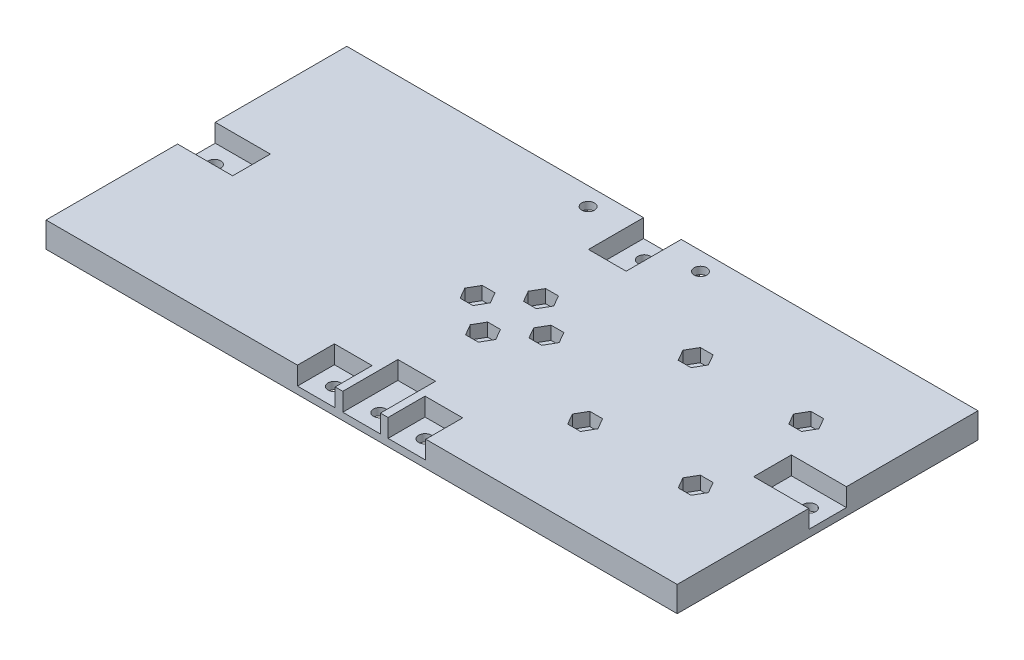
SolidWorks part; units mm, degrees
ref_plane "Front Plane" through (0, 0, 0) normal (0, 0, 1) x (1, 0, 0)
ref_plane "Top Plane" through (0, 0, 0) normal (0, 1, 0) x (1, 0, 0)
ref_plane "Right Plane" through (0, 0, 0) normal (1, 0, 0) x (0, 0, -1)
sketch "Sketch1" plane through (0, 0, 0) normal (0, 1, 0) x (1, 0, 0)
  line L1 (0, 0) -> (174.17, 0)
  line L2 (0, 0) -> (0, 83)
  line L3 (0, 83) -> (174.17, 83)
  line L4 (174.17, 0) -> (174.17, 83)
  dimension "D1" = 174.17
  dimension "D2" = 83
extrude "Boss-Extrude1" add sketch "Sketch1" along normal blind 7
sketch "Sketch2" plane through (0, 7, 0) normal (0, 1, 0) x (1, 0, 0)
  line L0 (0, 83) -> (174.17, 0) construction
  line L1 (77.585, 41.5) -> (96.585, 41.5) construction
  line L2 (87.085, 49.5) -> (87.085, 33.5) construction
  circle A0 centre (87.085, 49.5) radius 1.75
  circle A1 centre (77.585, 41.5) radius 1.75
  circle A2 centre (96.585, 41.5) radius 1.75
  circle A3 centre (87.085, 33.5) radius 1.75
  point P8 (87.085, 41.5)
  point P9 (87.085, 41.5)
  point P10 (87.085, 41.5)
  dimension "D3" = 3.5
  dimension "D1" = 19
  dimension "D2" = 16
extrude "Cut-Extrude1" cut sketch "Sketch2" against normal through all
sketch "Sketch3" plane through (0, 7, 0) normal (0, 1, 0) x (1, 0, 0)
  line L0 (0, 83) -> (174.17, 0) construction
  line L1 (5, 41.5) -> (169.17, 41.5) construction
  line L2 (87.085, 78) -> (87.085, 5) construction
  circle A0 centre (87.085, 78) radius 1.75
  circle A1 centre (5, 41.5) radius 1.75
  circle A2 centre (87.085, 5) radius 1.75
  circle A3 centre (169.17, 41.5) radius 1.75
  point P8 (87.085, 41.5)
  point P9 (87.085, 41.5)
  point P11 (87.085, 41.5)
  dimension "D3" = 3.5
  dimension "D1" = 164.17
  dimension "D2" = 73
extrude "Cut-Extrude2" cut sketch "Sketch3" against normal through all
sketch "Sketch4" plane through (0, 7, 0) normal (0, 1, 0) x (1, 0, 0)
  line L0 (0, 83) -> (0, 0) construction
  line L1 (0, 46.5) -> (15, 46.5) construction
  line L2 (0, 46.5) -> (0, 36.5) construction
  line L3 (0, 36.5) -> (15, 36.5) construction
  line L4 (15, 46.5) -> (15, 36.5) construction
  line L5 (0, 0) -> (174.17, 0) construction
  line L6 (82.085, 0) -> (92.085, 0) construction
  line L7 (82.085, 0) -> (82.085, 15) construction
  line L8 (82.085, 15) -> (92.085, 15) construction
  line L9 (92.085, 0) -> (92.085, 15) construction
  line L10 (174.17, 83) -> (0, 83) construction
  line L11 (92.085, 83) -> (82.085, 83) construction
  line L12 (92.085, 83) -> (92.085, 68) construction
  line L13 (92.085, 68) -> (82.085, 68) construction
  line L14 (82.085, 83) -> (82.085, 68) construction
  line L15 (174.17, 0) -> (174.17, 83) construction
  line L16 (174.17, 36.5) -> (159.17, 36.5) construction
  line L17 (174.17, 36.5) -> (174.17, 46.5) construction
  line L18 (174.17, 46.5) -> (159.17, 46.5) construction
  line L19 (159.17, 36.5) -> (159.17, 46.5) construction
  line L20 (0, 41.5) -> (174.17, 41.5) construction
  line L21 (87.085, 83) -> (87.085, 0) construction
  line L22 (-0.2, 46.7) -> (15.2, 46.7)
  line L23 (15.2, 46.7) -> (15.2, 36.3)
  line L24 (-0.2, 36.3) -> (15.2, 36.3)
  line L25 (-0.2, 46.7) -> (-0.2, 36.3)
  line L26 (81.885, 15.2) -> (92.285, 15.2)
  line L27 (92.285, -0.2) -> (92.285, 15.2)
  line L28 (81.885, -0.2) -> (92.285, -0.2)
  line L29 (81.885, -0.2) -> (81.885, 15.2)
  line L30 (81.885, 83.2) -> (81.885, 67.8)
  line L31 (92.285, 67.8) -> (81.885, 67.8)
  line L32 (92.285, 83.2) -> (92.285, 67.8)
  line L33 (92.285, 83.2) -> (81.885, 83.2)
  line L34 (174.37, 46.7) -> (158.97, 46.7)
  line L35 (158.97, 36.3) -> (158.97, 46.7)
  line L36 (174.37, 36.3) -> (158.97, 36.3)
  line L37 (174.37, 36.3) -> (174.37, 46.7)
  point P26 (87.085, 0)
  point P27 (0, 41.5)
  point P28 (87.085, 83)
  point P29 (174.17, 41.5)
  dimension "D1" = 15
  dimension "D2" = 10
  dimension "D3" = 0.2
extrude "Cut-Extrude3" cut sketch "Sketch4" against normal blind 5
sketch "Sketch5" plane through (0, 7, 0) normal (0, 1, 0) x (1, 0, 0)
  line L0 (0, 0) -> (81.885, 0) construction
  line L6 (79.585, 10) -> (79.585, 0) construction
  line L7 (79.585, 0) -> (69.585, 0) construction
  line L9 (79.585, 10) -> (69.585, 10) construction
  line L10 (69.585, 0) -> (69.585, 10) construction
  line L11 (94.585, 0) -> (104.585, 0) construction
  line L13 (94.585, 10) -> (104.585, 10) construction
  line L14 (104.585, 0) -> (104.585, 10) construction
  line L16 (92.285, 0) -> (174.17, 0) construction
  line L17 (94.585, 10) -> (94.585, 0) construction
  line L18 (79.585, 0) -> (94.585, 0) construction
  line L22 (87.085, 83) -> (87.085, 0) construction
  line L23 (92.285, 83) -> (81.885, 83) construction
  line L24 (79.785, 10.2) -> (69.385, 10.2)
  line L25 (69.385, -0.2) -> (69.385, 10.2)
  line L26 (79.785, -0.2) -> (69.385, -0.2)
  line L27 (79.785, 10.2) -> (79.785, -0.2)
  line L28 (94.385, 10.2) -> (104.785, 10.2)
  line L29 (104.785, -0.2) -> (104.785, 10.2)
  line L30 (94.385, -0.2) -> (104.785, -0.2)
  line L31 (94.385, 10.2) -> (94.385, -0.2)
  point P2 (87.085, 0)
  dimension "D1" = 15
  dimension "D2" = 0.2
  dimension "D3" = 10
  dimension "D4" = 10
  dimension "D5" = 10
  dimension "D6" = 10
extrude "Cut-Extrude4" cut sketch "Sketch5" against normal blind 5
sketch "Sketch6" plane through (0, 2, 0) normal (0, 1, 0) x (1, 0, 0)
  line L0 (74.585, 0) -> (74.585, 5) construction
  line L1 (79.785, 0) -> (69.385, 0) construction
  line L2 (99.585, 0) -> (99.585, 5) construction
  line L3 (94.385, 0) -> (104.785, 0) construction
  circle A0 centre (74.585, 5) radius 1.75
  circle A1 centre (99.585, 5) radius 1.75
  dimension "D3" = 3.5
  dimension "D4" = 3.5
  dimension "D1" = 5
  dimension "D2" = 5
extrude "Cut-Extrude5" cut sketch "Sketch6" against normal through all
sketch "ESC Reference" plane through (0, 0, 0) normal (0, -1, 0) x (1, 0, 0)
  line L0 (174.17, -41.5) -> (87.1154, -41.5) construction
  line L1 (116.7639, -20.5) -> (158.7639, -20.5) construction
  line L2 (116.7639, -20.5) -> (116.7639, -62.5) construction
  line L3 (116.7639, -62.5) -> (158.7639, -62.5) construction
  line L4 (158.7639, -20.5) -> (158.7639, -62.5) construction
  line L5 (122.5139, -26.25) -> (153.0139, -26.25) construction
  line L6 (122.5139, -26.25) -> (122.5139, -56.75) construction
  line L7 (122.5139, -56.75) -> (153.0139, -56.75) construction
  line L8 (153.0139, -26.25) -> (153.0139, -56.75) construction
  line L9 (174.17, 0) -> (174.17, -83) construction
  point P4 (159.4552, -57.2836)
  point P9 (158.7639, -41.5)
  point P10 (122.5139, -41.5)
  point P11 (116.7639, -41.5)
  point P12 (137.7639, -26.25)
  point P13 (137.7639, -20.5)
  point P14 (164.0651, -62.5)
  dimension "D1" = 42
  dimension "D2" = 42
  dimension "D3" = 30.5
  dimension "D4" = 30.5
  dimension "D5" = 21.1561
sketch "Sketch12" plane through (0, 0, 0) normal (0, -1, 0) x (1, 0, 0)
  circle A0 centre (122.5139, -26.25) radius 1.75
  circle A1 centre (153.0139, -26.25) radius 1.75
  circle A2 centre (122.5139, -56.75) radius 1.75
  circle A3 centre (153.0139, -56.75) radius 1.75
  dimension "D1" = 3.5
extrude "Cut-Extrude9" cut sketch "Sketch12" against normal through all
sketch "Sketch7" plane through (0, 7, 0) normal (0, 1, 0) x (1, 0, 0)
  line L0 (75.8241, 44.55) -> (79.3459, 44.55)
  line L1 (79.3459, 44.55) -> (81.1068, 41.5)
  line L2 (81.1068, 41.5) -> (79.3459, 38.45)
  line L3 (79.3459, 38.45) -> (75.8241, 38.45)
  line L4 (75.8241, 38.45) -> (74.0632, 41.5)
  line L5 (74.0632, 41.5) -> (75.8241, 44.55)
  line L6 (87.085, 33.5) -> (87.085, 49.5) construction
  line L7 (85.3241, 52.55) -> (88.8459, 52.55)
  line L8 (88.8459, 52.55) -> (90.6068, 49.5)
  line L9 (90.6068, 49.5) -> (88.8459, 46.45)
  line L10 (88.8459, 46.45) -> (85.3241, 46.45)
  line L11 (85.3241, 46.45) -> (83.5632, 49.5)
  line L12 (83.5632, 49.5) -> (85.3241, 52.55)
  line L13 (77.585, 41.5) -> (96.585, 41.5) construction
  line L14 (100.1068, 41.5) -> (98.3459, 44.55)
  line L15 (98.3459, 38.45) -> (100.1068, 41.5)
  line L16 (94.8241, 38.45) -> (98.3459, 38.45)
  line L17 (93.0632, 41.5) -> (94.8241, 38.45)
  line L18 (94.8241, 44.55) -> (93.0632, 41.5)
  line L19 (98.3459, 44.55) -> (94.8241, 44.55)
  line L20 (83.5632, 33.5) -> (85.3241, 30.45)
  line L21 (85.3241, 36.55) -> (83.5632, 33.5)
  line L22 (88.8459, 36.55) -> (85.3241, 36.55)
  line L23 (90.6068, 33.5) -> (88.8459, 36.55)
  line L24 (88.8459, 30.45) -> (90.6068, 33.5)
  line L25 (85.3241, 30.45) -> (88.8459, 30.45)
  line L26 (120.753, 29.3) -> (124.2749, 29.3)
  line L27 (124.2749, 29.3) -> (126.0358, 26.25)
  line L28 (126.0358, 26.25) -> (124.2749, 23.2)
  line L29 (124.2749, 23.2) -> (120.753, 23.2)
  line L30 (120.753, 23.2) -> (118.9921, 26.25)
  line L31 (118.9921, 26.25) -> (120.753, 29.3)
  line L32 (151.253, 29.3) -> (154.7749, 29.3)
  line L33 (154.7749, 29.3) -> (156.5358, 26.25)
  line L34 (156.5358, 26.25) -> (154.7749, 23.2)
  line L35 (154.7749, 23.2) -> (151.253, 23.2)
  line L36 (151.253, 23.2) -> (149.4921, 26.25)
  line L37 (149.4921, 26.25) -> (151.253, 29.3)
  line L38 (151.253, 59.8) -> (154.7749, 59.8)
  line L39 (154.7749, 59.8) -> (156.5358, 56.75)
  line L40 (156.5358, 56.75) -> (154.7749, 53.7)
  line L41 (154.7749, 53.7) -> (151.253, 53.7)
  line L42 (151.253, 53.7) -> (149.4921, 56.75)
  line L43 (149.4921, 56.75) -> (151.253, 59.8)
  line L44 (120.753, 59.8) -> (124.2749, 59.8)
  line L45 (124.2749, 59.8) -> (126.0358, 56.75)
  line L46 (126.0358, 56.75) -> (124.2749, 53.7)
  line L47 (124.2749, 53.7) -> (120.753, 53.7)
  line L48 (120.753, 53.7) -> (118.9921, 56.75)
  line L49 (118.9921, 56.75) -> (120.753, 59.8)
  circle A1 centre (77.585, 41.5) radius 3.5218 construction
  circle A2 centre (87.085, 49.5) radius 3.5218 construction
  circle A3 centre (96.585, 41.5) radius 3.5218 construction
  circle A4 centre (87.085, 33.5) radius 3.5218 construction
  circle A5 centre (122.5139, 26.25) radius 3.5218 construction
  circle A6 centre (153.0139, 26.25) radius 3.5218 construction
  circle A7 centre (153.0139, 56.75) radius 3.5218 construction
  circle A8 centre (122.5139, 56.75) radius 3.5218 construction
  point P11 (77.585, 38.45)
  point P24 (87.085, 46.45)
  point P46 (122.5139, 23.2)
  point P47 (122.5139, 26.25)
  point P57 (153.0139, 23.2)
  point P58 (153.0139, 26.25)
  point P68 (153.0139, 53.7)
  point P69 (153.0139, 56.75)
  point P79 (122.5139, 53.7)
  point P80 (122.5139, 56.75)
  point P82 (122.5139, 56.75)
  dimension "D1" = 120
  dimension "D2" = 6.1
  dimension "D3" = 120
  dimension "D4" = 6.1
  dimension "D5" = 120
  dimension "D6" = 6.1
  dimension "D7" = 120
  dimension "D8" = 6.1
  dimension "D9" = 120
  dimension "D10" = 6.1
  dimension "D11" = 120
  dimension "D12" = 6.1
extrude "Cut-Extrude6" cut sketch "Sketch7" against normal blind 3.64
sketch "Sketch9" plane through (0, 0, 0) normal (0, -1, 0) x (1, 0, 0)
  line L0 (174.17, -83) -> (0, -83) construction
  line L1 (66.585, -83) -> (76.585, -83) construction
  line L2 (66.585, -83) -> (66.585, -73) construction
  line L3 (66.585, -73) -> (76.585, -73) construction
  line L4 (76.585, -83) -> (76.585, -73) construction
  line L5 (66.585, -73) -> (76.585, -83) construction
  line L6 (97.585, -83) -> (107.585, -83) construction
  line L7 (97.585, -83) -> (97.585, -73) construction
  line L8 (97.585, -73) -> (107.585, -73) construction
  line L9 (107.585, -83) -> (107.585, -73) construction
  line L10 (97.585, -73) -> (107.585, -83) construction
  line L11 (66.385, -72.8) -> (76.785, -72.8)
  line L12 (76.785, -83.2) -> (76.785, -72.8)
  line L13 (66.385, -83.2) -> (76.785, -83.2)
  line L14 (66.385, -83.2) -> (66.385, -72.8)
  line L15 (97.385, -72.8) -> (107.785, -72.8)
  line L16 (107.785, -83.2) -> (107.785, -72.8)
  line L17 (97.385, -83.2) -> (107.785, -83.2)
  line L18 (97.385, -83.2) -> (97.385, -72.8)
  line L19 (87.085, -83) -> (87.085, 0) construction
  line L20 (0, 0) -> (174.17, 0) construction
  line L21 (102.585, -78) -> (71.585, -78) construction
  point P10 (71.585, -78)
  point P11 (102.585, -78)
  point P12 (87.085, -78)
  dimension "D1" = 10
  dimension "D2" = 10
  dimension "D3" = 31
  dimension "D5" = 0.2
extrude "Cut-Extrude7" cut sketch "Sketch9" against normal blind 5
sketch "Sketch10" plane through (0, 5, 0) normal (0, -1, 0) x (1, 0, 0)
  line L0 (66.585, -73) -> (76.585, -83) construction
  line L1 (97.585, -73) -> (107.585, -83) construction
  circle A0 centre (71.585, -78) radius 1.75
  circle A1 centre (102.585, -78) radius 1.75
  dimension "D1" = 3.5
extrude "Cut-Extrude8" cut sketch "Sketch10" against normal through all
